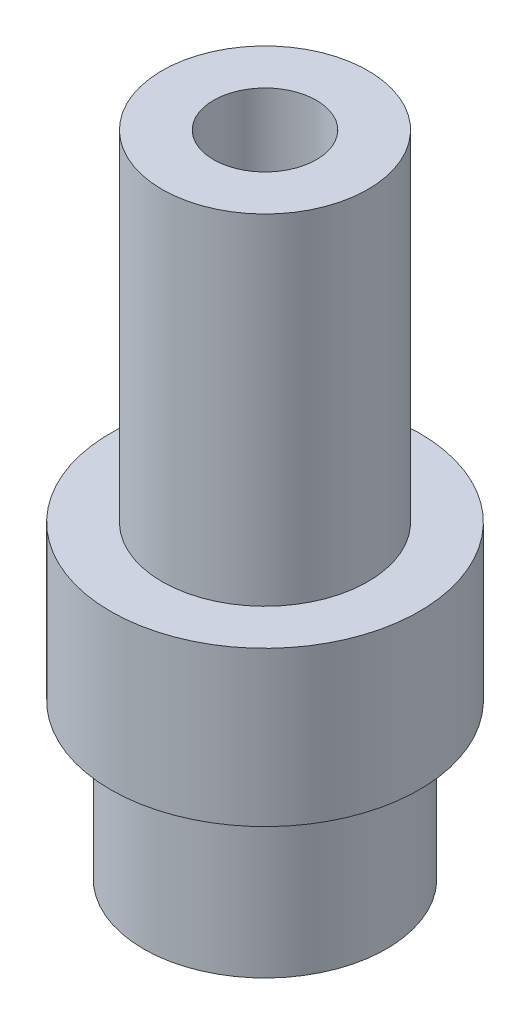
SolidWorks part; units mm, degrees
ref_plane "Front Plane" through (0, 0, 0) normal (0, 0, 1) x (1, 0, 0)
ref_plane "Top Plane" through (0, 0, 0) normal (0, 1, 0) x (1, 0, 0)
ref_plane "Right Plane" through (0, 0, 0) normal (1, 0, 0) x (0, 0, -1)
sketch "Sketch1" plane through (0, 0, 0) normal (0, 0, 1) x (1, 0, 0)
  line L0 (-3.175, 0) -> (-6.35, 0)
  line L1 (-6.35, 0) -> (-6.35, -20.955)
  line L2 (-6.35, -20.955) -> (-9.525, -20.955)
  line L3 (-9.525, -20.955) -> (-9.525, -30.48)
  line L4 (-9.525, -30.48) -> (-7.493, -30.48)
  line L5 (-7.493, -30.48) -> (-7.493, -40.005)
  line L6 (-7.493, -40.005) -> (-5.207, -40.005)
  line L7 (-5.207, -40.005) -> (-5.207, -27.305)
  line L8 (-5.207, -27.305) -> (-3.175, -27.305)
  line L9 (-3.175, -27.305) -> (-3.175, 0)
  line L10 (0, 0) -> (0, -16.6803) construction
  dimension "D1" = 12.7
  dimension "D2" = 3.175
  dimension "D3" = 9.525
  dimension "D4" = 6.35
  dimension "D5" = 2.032
  dimension "D6" = 2.032
  dimension "D7" = 20.955
  dimension "D8" = 9.525
  dimension "D9" = 19.05
revolve "Revolve1" add sketch "Sketch1" angle 360 about L10
